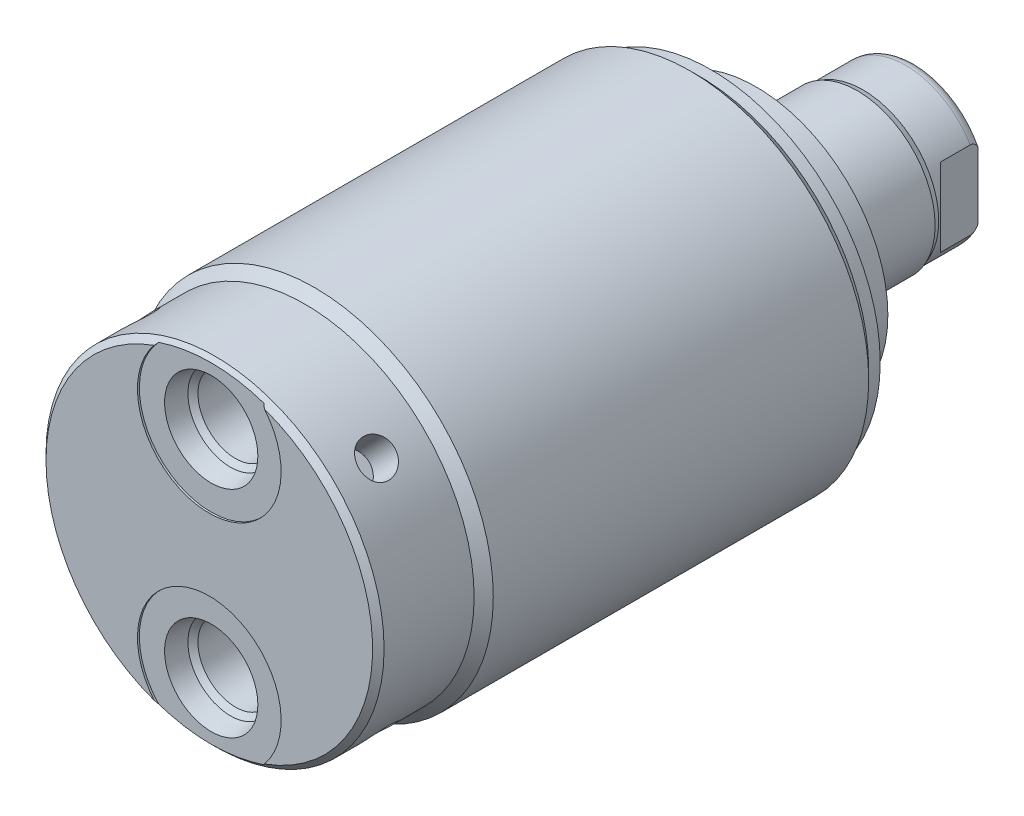
SolidWorks part; units mm, degrees
material "Alloy Steel"
ref_plane "Front Plane" through (0, 0, 0) normal (0, 0, 1) x (1, 0, 0)
ref_plane "Top Plane" through (0, 0, 0) normal (0, 1, 0) x (1, 0, 0)
ref_plane "Right Plane" through (0, 0, 0) normal (1, 0, 0) x (0, 0, -1)
ref_plane "Plane1" through (0, 0, 0) normal (0, 0, 1) x (1, 0, 0)
sketch "Sketch1" plane through (0, 0, 0) normal (0, 0, 1) x (1, 0, 0)
  circle A0 centre (0, 0) radius 23.6855
  dimension "D1" = 47.371
extrude "Extrude1" add sketch "Sketch1" along normal blind 66.548
sketch "Sketch2" plane through (0, 0, 0) normal (0, 1, 0) x (1, 0, 0)
  line L0 (23.6855, -66.548) -> (23.6855, -52.578)
  line L1 (23.6855, -52.578) -> (22.4155, -53.848)
  line L2 (22.4155, -53.848) -> (22.4155, -66.548)
  line L3 (22.4155, -66.548) -> (23.6855, -66.548)
  line L4 (0, 0) -> (0, -24.4965) construction
  line L5 (-23.6855, -66.548) -> (23.6855, -66.548) construction
  line L6 (23.6855, -66.548) -> (23.6855, 0) construction
  dimension "D1" = 12.7
  dimension "D2" = 44.831
  dimension "D3" = 45
revolve "Cut-Revolve1" cut sketch "Sketch2" angle 360 about L4
sketch "Sketch3" plane through (0, 0, 0) normal (0, 1, 0) x (1, 0, 0)
  line L0 (22.4155, 0) -> (22.4155, -1.524)
  line L1 (22.4155, -1.524) -> (23.6855, -2.794)
  line L2 (23.6855, -2.794) -> (23.6855, 0)
  line L3 (23.6855, 0) -> (22.4155, 0)
  line L4 (0, 0) -> (0, 3.0455) construction
  line L5 (22.4155, -66.548) -> (22.4155, -53.848) construction
  line L6 (23.6855, 0) -> (-23.6855, 0) construction
  line L7 (23.6855, -52.578) -> (23.6855, 0) construction
  dimension "D1" = 45
  dimension "D2" = 1.524
revolve "Cut-Revolve2" cut sketch "Sketch3" angle 360 about L4
chamfer "Chamfer1" distance 0.762 angle 45 1 edges at (-22.4155, 0, 66.548)
sketch "S2D0002" plane through (0, 0, 0) normal (1, 0, 0) x (0, -1, 0)
  line L0 (20.4597, -66.294) -> (23.7998, -66.294)
  line L1 (20.4597, -66.294) -> (19.9171, -63.7413)
  line L2 (19.9171, -63.7413) -> (19.2532, -63.0774)
  line L3 (19.2532, -63.0774) -> (19.2532, -52.324)
  line L4 (19.2532, -52.324) -> (14.2748, -52.324)
  line L5 (14.2748, -52.324) -> (14.2748, -66.548)
  line L6 (14.2748, -14.6685) -> (14.2748, 0.6985) construction
  line L8 (23.7998, -66.294) -> (23.7998, -66.548)
  line L9 (-22.4155, -66.548) -> (22.4155, -66.548) construction
  line L10 (23.7998, -66.548) -> (14.2748, -66.548)
  dimension "D1" = 19.05
  dimension "D2" = 9.9568
  dimension "D3" = 0.254
  dimension "D4" = 12.3698
  dimension "D5" = 12
  dimension "D6" = 45
  dimension "D7" = 2.5527
  dimension "D8" = 13.97
  dimension "D9" = 14.2748
revolve "Cut-Revolve3" cut sketch "S2D0002" angle 360 about L6
sketch "Sketch6" plane through (0, 0, 0) normal (0, 0, -1) x (-1, 0, 0)
  circle A0 centre (0, 0) radius 17.4625
  circle A1 centre (0, 0) radius 23.6855 construction
  dimension "D1" = 34.925
extrude "Extrude2" add sketch "Sketch6" along normal blind 5.969
sketch "Sketch7" plane through (0, 0, 0) normal (1, 0, 0) x (0, 0, -1)
  line L0 (5.969, 0) -> (5.969, -10.3187)
  line L1 (5.969, -10.3187) -> (26.797, -10.3187)
  line L2 (26.797, -10.3187) -> (26.797, 0)
  line L3 (26.797, 0) -> (5.969, 0)
  line L4 (0, 0) -> (9.7123, 0) construction
  line L5 (5.969, -17.4625) -> (5.969, 17.4625) construction
  dimension "D1" = 20.6375
  dimension "D2" = 20.828
revolve "Revolve1" add sketch "Sketch7" angle 360 about L4
sketch "S2D0001" plane through (0, 0, 0) normal (0, 1, 0) x (1, 0, 0)
  line L0 (3.2639, 24.8613) -> (3.2639, 11.9888)
  line L1 (3.2639, 11.9888) -> (0, 11.9888)
  line L2 (4.3815, 26.797) -> (0, 26.797)
  line L3 (0, 26.797) -> (0, 11.9888)
  line L4 (3.2639, 24.8613) -> (4.3815, 26.797)
  line L5 (0, -31.3084) -> (0, 2.765) construction
  line L6 (10.3188, 26.797) -> (-10.3188, 26.797) construction
  dimension "D1" = 8.763
  dimension "D2" = 30
  dimension "D3" = 14.8082
  dimension "D4" = 6.5278
revolve "Cut-Revolve5" cut sketch "S2D0001" angle 360 about L5
ref_plane "Plane8" through (0, 0, 0) normal (1, 0, 0) x (0, -1, 0)
sketch "Sketch9" plane through (0, 0, 0) normal (1, 0, 0) x (0, -1, 0)
  line L0 (-10.3188, 19.3802) -> (-10.033, 20.1422)
  line L1 (-10.033, 20.1422) -> (-10.033, 25.781)
  line L2 (0, 12.6594) -> (0, 20.8178) construction
  line L3 (10.3187, 26.797) -> (-10.3188, 26.797) construction
  line L4 (-9.6449, 26.797) -> (-10.3188, 26.797)
  line L5 (-10.3188, 26.797) -> (-10.3188, 19.3802)
  arc A0 (-9.6449, 26.797) -> (-10.033, 25.781) centre (-8.509, 25.781) ccw
  dimension "D1" = 1.524
  dimension "D2" = 1.016
  dimension "D3" = 20.066
  dimension "D4" = 0.762
  dimension "D5" = 7.4168
revolve "Cut-Revolve6" cut sketch "Sketch9" angle 360 about L2
sketch "Sketch13" plane through (0, 0, 0) normal (0, 1, 0) x (1, 0, 0)
  line L0 (8.5852, 26.797) -> (8.5852, 21.844)
  line L1 (8.5852, 21.844) -> (10.033, 20.3962)
  line L2 (-8.5852, 26.797) -> (-8.5852, 21.844)
  line L3 (-8.5852, 21.844) -> (-10.033, 20.3962)
  line L4 (9.6449, 26.797) -> (-9.6449, 26.797) construction
  line L5 (0, 13.7262) -> (0, 20.767) construction
  line L6 (10.033, 20.3962) -> (10.033, 26.797)
  line L8 (8.5852, 26.797) -> (10.033, 26.797)
  line L9 (10.033, 20.1422) -> (10.033, 25.781) construction
  line L10 (-10.033, 20.3962) -> (-10.033, 26.797)
  line L11 (-8.5852, 26.797) -> (-10.033, 26.797)
  dimension "D1" = 17.1704
  dimension "D2" = 135
  dimension "D3" = 4.953
extrude "Cut-Extrude4" cut sketch "Sketch13" against normal mid plane 39.685
ref_plane "Plane13" through (0, 0, 0) normal (0.7071, 0.7071, 0) x (0, 0, -1)
hole_wizard "Hole1" positions "3DSketch2" profile "Sketch14" legacy
sketch3d "3DSketch2"
  point P0 (-15.8502, 15.8502, 60.198)
  dimension "D1" = 6.35
sketch "Sketch14" plane through (-15.8502, 15.8502, 60.198) normal (0, 0, 1) x (-0.7071, -0.7071, 0)
  line L0 (0, 0) -> (0, 4.7498)
  line L1 (0, 4.7498) -> (2.3749, 4.7498)
  line L2 (2.3749, 4.7498) -> (2.3749, 0)
  line L3 (2.3749, 0) -> (0, 0)
  line L4 (0, 110) -> (0, -10) construction
  dimension "Diameter" = 4.7498
  dimension "Depth" = 4.7498
pattern_circular "CirPattern1" count 4 over 360 about axis through (0, 0, 0) along (0, 0, 1) of "Hole1"
pattern_linear "LPattern1" count 2 spacing 28.5496 along (0, 1, 0) of "Cut-Revolve3"
